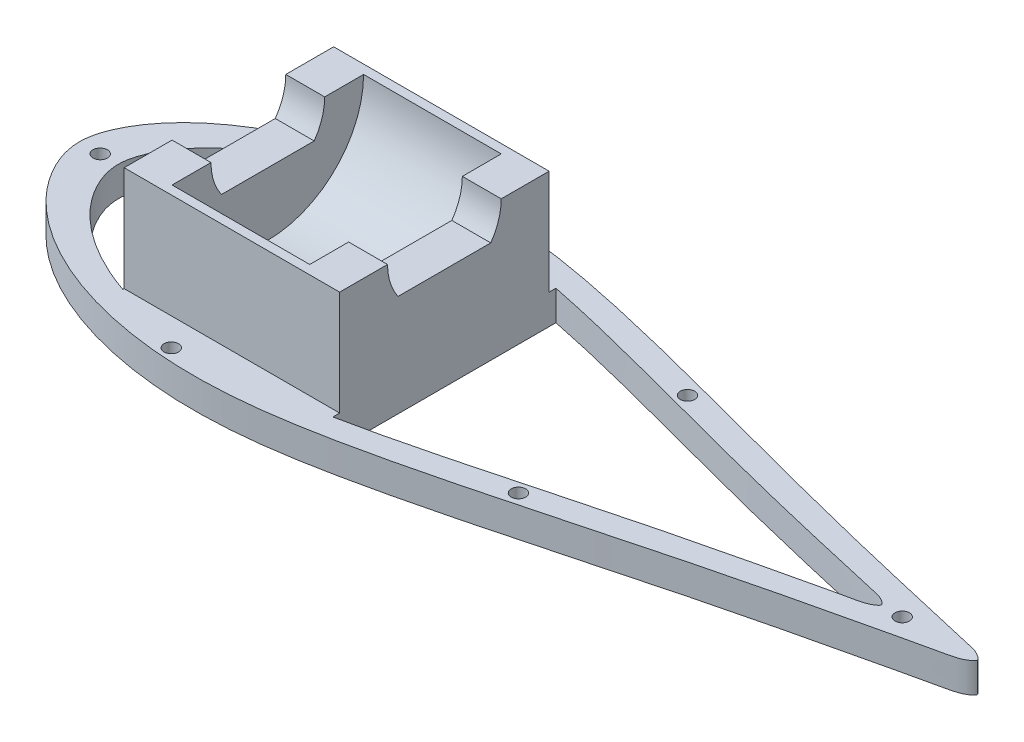
SolidWorks part; units mm, degrees
material "6061 Alloy"
ref_plane "Front Plane" through (0, 0, 0) normal (0, 0, 1) x (1, 0, 0)
ref_plane "Top Plane" through (0, 0, 0) normal (0, 1, 0) x (1, 0, 0)
ref_plane "Right Plane" through (0, 0, 0) normal (1, 0, 0) x (0, 0, -1)
curve "Curve2"
  spline degree 3 poles (0.6483, 0, -5.7987) (-0.3085, 0, 0) (0.6483, 0, 5.7987) (3.0311, 0, 11.5336) (6.6533, 0, 17.267) (11.4717, 0, 22.8371) (17.4302, 0, 28.1154) (24.4659, 0, 32.9986) (32.5279, 0, 37.3723) (41.5389, 0, 41.1607) (51.4314, 0, 44.2651) (62.1158, 0, 46.6282) (73.526, 0, 48.1549) (85.6114, 0, 48.7284) (98.3426, 0, 48.3105) (111.7257, 0, 46.8479) (125.7606, 0, 44.4122) (140.4343, 0, 41.2887) (155.6347, 0, 37.6615) (171.177, 0, 33.6995) (186.8539, 0, 29.5664) (202.4318, 0, 25.4194) (217.9957, 0, 21.2663) (233.2084, 0, 17.405) (247.6838, 0, 13.8748) (260.7251, 0, 10.7897) (272.1052, 0, 8.143) (281.7116, 0, 5.9794) (289.2075, 0, 4.169) (295.0367, 0, 3.0969) (298.1709, 0, 1.895) (300.5776, 0, 0) (298.1709, 0, -1.895) (295.0367, 0, -3.0969) (289.2075, 0, -4.169) (281.7116, 0, -5.9794) (272.1052, 0, -8.143) (260.7251, 0, -10.7897) (247.6838, 0, -13.8748) (233.2084, 0, -17.405) (217.9957, 0, -21.2663) (202.4318, 0, -25.4194) (186.8539, 0, -29.5664) (171.177, 0, -33.6995) (155.6347, 0, -37.6615) (140.4343, 0, -41.2887) (125.7606, 0, -44.4122) (111.7257, 0, -46.8479) (98.3426, 0, -48.3105) (85.6114, 0, -48.7284) (73.526, 0, -48.1549) (62.1158, 0, -46.6282) (51.4314, 0, -44.2651) (41.5389, 0, -41.1607) (32.5279, 0, -37.3723) (24.4659, 0, -32.9986) (17.4302, 0, -28.1154) (11.4717, 0, -22.8371) (6.6533, 0, -17.267) (3.0311, 0, -11.5336) (0.6483, 0, -5.7987) (-0.3085, 0, 0) (0.6483, 0, 5.7987) knots -0.028335 -0.018012 -0.008569 0 0.008569 0.018012 0.028335 0.039554 0.051691 0.064762 0.078763 0.093696 0.109541 0.126268 0.143841 0.162293 0.181715 0.202223 0.224008 0.247042 0.271046 0.295702 0.320629 0.34543 0.369662 0.394535 0.417436 0.438027 0.456004 0.47109 0.483065 0.49175 0.497395 0.5 0.502605 0.50825 0.516935 0.52891 0.543996 0.561973 0.582564 0.605465 0.630338 0.65457 0.679371 0.704298 0.728954 0.752958 0.775992 0.797777 0.818285 0.837707 0.856159 0.873732 0.890459 0.906304 0.921237 0.935238 0.948309 0.960446 0.971665 0.981988 0.991431 1 1.008569 1.018012 1.028335 periodic
sketch "Sketch3" plane through (0, 0, 0) normal (0, 1, 0) x (1, 0, 0)
  spline S0 degree 3 poles (0.6483, 5.7987) (-0.3085, 0) (0.6483, -5.7987) (3.0311, -11.5336) (6.6533, -17.267) (11.4717, -22.8371) (17.4302, -28.1154) (24.4659, -32.9986) (32.5279, -37.3723) (41.5389, -41.1607) (51.4314, -44.2651) (62.1158, -46.6282) (73.526, -48.1549) (85.6114, -48.7284) (98.3426, -48.3105) (111.7257, -46.8479) (125.7606, -44.4122) (140.4343, -41.2887) (155.6347, -37.6615) (171.177, -33.6995) (186.8539, -29.5664) (202.4318, -25.4194) (217.9957, -21.2663) (233.2084, -17.405) (247.6838, -13.8748) (260.7251, -10.7897) (272.1052, -8.143) (281.7116, -5.9794) (289.2075, -4.169) (295.0367, -3.0969) (298.1709, -1.895) (300.5776, 0) (298.1709, 1.895) (295.0367, 3.0969) (289.2075, 4.169) (281.7116, 5.9794) (272.1052, 8.143) (260.7251, 10.7897) (247.6838, 13.8748) (233.2084, 17.405) (217.9957, 21.2663) (202.4318, 25.4194) (186.8539, 29.5664) (171.177, 33.6995) (155.6347, 37.6615) (140.4343, 41.2887) (125.7606, 44.4122) (111.7257, 46.8479) (98.3426, 48.3105) (85.6114, 48.7284) (73.526, 48.1549) (62.1158, 46.6282) (51.4314, 44.2651) (41.5389, 41.1607) (32.5279, 37.3723) (24.4659, 32.9986) (17.4302, 28.1154) (11.4717, 22.8371) (6.6533, 17.267) (3.0311, 11.5336) (0.6483, 5.7987) (-0.3085, 0) (0.6483, -5.7987) knots -0.028335 -0.018012 -0.008569 0 0.008569 0.018012 0.028335 0.039554 0.051691 0.064762 0.078763 0.093696 0.109541 0.126268 0.143841 0.162293 0.181715 0.202223 0.224008 0.247042 0.271046 0.295702 0.320629 0.34543 0.369662 0.394535 0.417436 0.438027 0.456004 0.47109 0.483065 0.49175 0.497395 0.5 0.502605 0.50825 0.516935 0.52891 0.543996 0.561973 0.582564 0.605465 0.630338 0.65457 0.679371 0.704298 0.728954 0.752958 0.775992 0.797777 0.818285 0.837707 0.856159 0.873732 0.890459 0.906304 0.921237 0.935238 0.948309 0.960446 0.971665 0.981988 0.991431 1 1.008569 1.018012 1.028335 only from (0, 0) to (0, 0) construction
  spline S1 degree 3 poles (0.6483, 5.7987) (-0.3085, 0) (0.6483, -5.7987) (3.0311, -11.5336) (6.6533, -17.267) (11.4717, -22.8371) (17.4302, -28.1154) (24.4659, -32.9986) (32.5279, -37.3723) (41.5389, -41.1607) (51.4314, -44.2651) (62.1158, -46.6282) (73.526, -48.1549) (85.6114, -48.7284) (98.3426, -48.3105) (111.7257, -46.8479) (125.7606, -44.4122) (140.4343, -41.2887) (155.6347, -37.6615) (171.177, -33.6995) (186.8539, -29.5664) (202.4318, -25.4194) (217.9957, -21.2663) (233.2084, -17.405) (247.6838, -13.8748) (260.7251, -10.7897) (272.1052, -8.143) (281.7116, -5.9794) (289.2075, -4.169) (295.0367, -3.0969) (298.1709, -1.895) (300.5776, 0) (298.1709, 1.895) (295.0367, 3.0969) (289.2075, 4.169) (281.7116, 5.9794) (272.1052, 8.143) (260.7251, 10.7897) (247.6838, 13.8748) (233.2084, 17.405) (217.9957, 21.2663) (202.4318, 25.4194) (186.8539, 29.5664) (171.177, 33.6995) (155.6347, 37.6615) (140.4343, 41.2887) (125.7606, 44.4122) (111.7257, 46.8479) (98.3426, 48.3105) (85.6114, 48.7284) (73.526, 48.1549) (62.1158, 46.6282) (51.4314, 44.2651) (41.5389, 41.1607) (32.5279, 37.3723) (24.4659, 32.9986) (17.4302, 28.1154) (11.4717, 22.8371) (6.6533, 17.267) (3.0311, 11.5336) (0.6483, 5.7987) (-0.3085, 0) (0.6483, -5.7987) knots -0.028335 -0.018012 -0.008569 0 0.008569 0.018012 0.028335 0.039554 0.051691 0.064762 0.078763 0.093696 0.109541 0.126268 0.143841 0.162293 0.181715 0.202223 0.224008 0.247042 0.271046 0.295702 0.320629 0.34543 0.369662 0.394535 0.417436 0.438027 0.456004 0.47109 0.483065 0.49175 0.497395 0.5 0.502605 0.50825 0.516935 0.52891 0.543996 0.561973 0.582564 0.605465 0.630338 0.65457 0.679371 0.704298 0.728954 0.752958 0.775992 0.797777 0.818285 0.837707 0.856159 0.873732 0.890459 0.906304 0.921237 0.935238 0.948309 0.960446 0.971665 0.981988 0.991431 1 1.008569 1.018012 1.028335 only from (0, 0) to (0, 0)
extrude "Boss-Extrude1" add sketch "Sketch3" along normal blind 10
sketch "Sketch4" plane through (0, 0, 0) normal (0, -1, 0) x (1, 0, 0)
  spline S1 degree 3 poles (299.9957, 0.014) (299.9938, -0.0895) (299.9638, -0.2086) (299.9031, -0.3373) (299.8291, -0.4596) (299.7174, -0.5996) (299.5918, -0.7263) (299.4861, -0.8218) (299.4046, -0.8909) (299.3213, -0.9578) (299.2087, -1.0447) (299.0654, -1.1499) (298.8903, -1.2715) (298.7126, -1.3891) (298.3525, -1.6168) (297.92, -1.8622) (297.411, -2.1134) (297.0223, -2.287) (296.6272, -2.4451) (296.2267, -2.5893) (295.822, -2.722) (295.4141, -2.8452) (295.0041, -2.961) (294.5925, -3.0704) (294.0419, -3.2092) (293.4889, -3.3386) (292.9344, -3.4614) (292.5179, -3.5509) (292.101, -3.6386) (291.5448, -3.754) (290.9884, -3.8677) (290.4319, -3.9815) (289.8757, -4.0959) (289.1809, -4.2414) (288.3483, -4.4216) (286.6852, -4.7905) (284.1958, -5.3676) (281.4314, -6.0157) (279.2189, -6.5298) (277.0055, -7.0405) (274.7915, -7.5479) (272.5773, -8.0547) (270.9166, -8.4349) (269.2562, -8.816) (267.0427, -9.3258) (264.2767, -9.9669) (259.8527, -10.9999) (254.3255, -12.3029) (248.8019, -13.6215) (244.3858, -14.6874) (239.9714, -15.7609) (234.4573, -17.1179) (228.9488, -18.4974) (224.5457, -19.6156) (217.945, -21.3082) (208.0596, -23.9078) (194.8919, -27.424) (183.9159, -30.3428) (175.1284, -32.6526) (166.3345, -34.9377) (158.628, -36.8918) (152.0088, -38.511) (148.6961, -39.3081) (145.3801, -40.0913) (142.0605, -40.8591) (138.737, -41.6097) (135.4091, -42.3409) (132.0764, -43.0503) (127.626, -43.9641) (122.0492, -45.0405) (113.0926, -46.5738) (104.0773, -47.7374) (95.0123, -48.3913) (88.1991, -48.6052) (81.3834, -48.5233) (74.5794, -48.1282) (67.8019, -47.4032) (61.0693, -46.3378) (54.4011, -44.9234) (47.8168, -43.1503) (41.3469, -40.998) (35.028, -38.4414) (28.8957, -35.456) (23.013, -32.0075) (18.3744, -28.7213) (14.8691, -25.8285) (12.3582, -23.5227) (9.984, -21.0765) (8.1373, -18.9185) (6.7509, -17.1189) (5.7603, -15.7327) (4.8235, -14.3098) (3.9449, -12.8503) (3.2654, -11.6036) (2.7565, -10.5882) (2.0291, -9.0471) (1.0809, -6.6677) (0.2183, -3.3645) (-0.1054, 0.0396) (0.2336, 3.4379) (0.961, 6.1924) (1.7397, 8.3272) (2.4132, 9.8934) (3.1645, 11.4234) (3.9845, 12.9173) (4.8661, 14.375) (6.1184, 16.2702) (8.4977, 19.4595) (11.5773, 22.8096) (14.9283, 25.8792) (17.5601, 28.0457) (20.2943, 30.0805) (22.6482, 31.6695) (24.5714, 32.8789) (26.5195, 34.0477) (29.9892, 35.9887) (35.0983, 38.4733) (41.419, 41.0252) (46.8122, 42.8146) (51.1842, 44.0565) (55.5891, 45.1756) (63.3708, 46.8228) (74.6452, 48.3036) (88.2816, 48.7503) (101.9024, 48.0274) (113.1705, 46.5598) (122.1264, 45.0264) (128.8176, 43.735) (135.487, 42.3362) (142.1376, 40.8488) (148.7724, 39.2926) (157.6025, 37.1514) (173.0143, 33.2397) (190.5764, 28.5711) (208.1372, 23.899) (221.3117, 20.4089) (234.5313, 17.0929) (245.5623, 14.3906) (254.4011, 12.2854) (261.0337, 10.722) (266.5649, 9.436) (270.9921, 8.4173) (274.3131, 7.6559) (277.6343, 6.8948) (280.9537, 6.1266) (284.2713, 5.3501) (287.59, 4.5785) (290.368, 3.9915) (292.5952, 3.5417) (294.2576, 3.1677) (295.6314, 2.798) (296.7027, 2.4227) (297.4846, 2.0873) (298.1125, 1.7565) (298.5991, 1.4632) (298.8968, 1.2692) (299.1297, 1.1058) (299.3003, 0.9778) (299.438, 0.8649) (299.5442, 0.7698) (299.6215, 0.6957) (299.6958, 0.6184) (299.7894, 0.5104) (299.8729, 0.3935) (299.9377, 0.2672) (299.9677, 0.1847) (299.984, 0.117) (299.9921, 0.0657) (299.9957, 0.014) (299.9938, -0.0895) (299.9638, -0.2086) knots -0.000244 -0.000163 -0.000081 0 0.000326 0.000488 0.000651 0.000977 0.001302 0.001465 0.001628 0.00179 0.001953 0.002279 0.002604 0.00293 0.003255 0.004557 0.005208 0.005859 0.00651 0.007161 0.007812 0.008464 0.009115 0.009766 0.010417 0.011719 0.01237 0.013021 0.013672 0.014323 0.015625 0.016276 0.016927 0.018229 0.019531 0.020833 0.026042 0.03125 0.033854 0.036458 0.041667 0.044271 0.046875 0.049479 0.052083 0.057292 0.0625 0.072917 0.083333 0.088542 0.09375 0.104167 0.114583 0.119792 0.125 0.145833 0.166667 0.1875 0.197917 0.208333 0.229167 0.234375 0.239583 0.244792 0.25 0.255208 0.260417 0.265625 0.270833 0.28125 0.291667 0.3125 0.322917 0.333333 0.34375 0.354167 0.364583 0.375 0.385417 0.395833 0.40625 0.416667 0.427083 0.4375 0.447917 0.453125 0.458333 0.463542 0.46875 0.471354 0.473958 0.476562 0.479167 0.481771 0.483073 0.484375 0.489583 0.494792 0.5 0.505208 0.510417 0.513021 0.515625 0.518229 0.520833 0.523438 0.526042 0.53125 0.541667 0.546875 0.552083 0.557292 0.5625 0.565104 0.567708 0.572917 0.583333 0.59375 0.604167 0.609375 0.614583 0.625 0.645833 0.666667 0.6875 0.708333 0.71875 0.729167 0.739583 0.75 0.760417 0.770833 0.791667 0.833333 0.854167 0.875 0.895833 0.916667 0.927083 0.9375 0.947917 0.953125 0.958333 0.963542 0.96875 0.973958 0.979167 0.984375 0.986979 0.989583 0.992188 0.99349 0.994792 0.996094 0.996745 0.997396 0.997721 0.998047 0.998372 0.998535 0.998698 0.998861 0.999023 0.999349 0.999512 0.999674 0.999756 0.999837 0.999919 1 1.000326 1.000488 1.000651 only from (299.9939, -0.0377) to (299.9939, -0.0377)
  spline S3 degree 3 poles (299.9957, 0.014) (299.9938, -0.0895) (299.9638, -0.2086) (299.9031, -0.3373) (299.8291, -0.4596) (299.7174, -0.5996) (299.5918, -0.7263) (299.4861, -0.8218) (299.4046, -0.8909) (299.3213, -0.9578) (299.2087, -1.0447) (299.0654, -1.1499) (298.8903, -1.2715) (298.7126, -1.3891) (298.3525, -1.6168) (297.92, -1.8622) (297.411, -2.1134) (297.0223, -2.287) (296.6272, -2.4451) (296.2267, -2.5893) (295.822, -2.722) (295.4141, -2.8452) (295.0041, -2.961) (294.5925, -3.0704) (294.0419, -3.2092) (293.4889, -3.3386) (292.9344, -3.4614) (292.5179, -3.5509) (292.101, -3.6386) (291.5448, -3.754) (290.9884, -3.8677) (290.4319, -3.9815) (289.8757, -4.0959) (289.1809, -4.2414) (288.3483, -4.4216) (286.6852, -4.7905) (284.1958, -5.3676) (281.4314, -6.0157) (279.2189, -6.5298) (277.0055, -7.0405) (274.7915, -7.5479) (272.5773, -8.0547) (270.9166, -8.4349) (269.2562, -8.816) (267.0427, -9.3258) (264.2767, -9.9669) (259.8527, -10.9999) (254.3255, -12.3029) (248.8019, -13.6215) (244.3858, -14.6874) (239.9714, -15.7609) (234.4573, -17.1179) (228.9488, -18.4974) (224.5457, -19.6156) (217.945, -21.3082) (208.0596, -23.9078) (194.8919, -27.424) (183.9159, -30.3428) (175.1284, -32.6526) (166.3345, -34.9377) (158.628, -36.8918) (152.0088, -38.511) (148.6961, -39.3081) (145.3801, -40.0913) (142.0605, -40.8591) (138.737, -41.6097) (135.4091, -42.3409) (132.0764, -43.0503) (127.626, -43.9641) (122.0492, -45.0405) (113.0926, -46.5738) (104.0773, -47.7374) (95.0123, -48.3913) (88.1991, -48.6052) (81.3834, -48.5233) (74.5794, -48.1282) (67.8019, -47.4032) (61.0693, -46.3378) (54.4011, -44.9234) (47.8168, -43.1503) (41.3469, -40.998) (35.028, -38.4414) (28.8957, -35.456) (23.013, -32.0075) (18.3744, -28.7213) (14.8691, -25.8285) (12.3582, -23.5227) (9.984, -21.0765) (8.1373, -18.9185) (6.7509, -17.1189) (5.7603, -15.7327) (4.8235, -14.3098) (3.9449, -12.8503) (3.2654, -11.6036) (2.7565, -10.5882) (2.0291, -9.0471) (1.0809, -6.6677) (0.2183, -3.3645) (-0.1054, 0.0396) (0.2336, 3.4379) (0.961, 6.1924) (1.7397, 8.3272) (2.4132, 9.8934) (3.1645, 11.4234) (3.9845, 12.9173) (4.8661, 14.375) (6.1184, 16.2702) (8.4977, 19.4595) (11.5773, 22.8096) (14.9283, 25.8792) (17.5601, 28.0457) (20.2943, 30.0805) (22.6482, 31.6695) (24.5714, 32.8789) (26.5195, 34.0477) (29.9892, 35.9887) (35.0983, 38.4733) (41.419, 41.0252) (46.8122, 42.8146) (51.1842, 44.0565) (55.5891, 45.1756) (63.3708, 46.8228) (74.6452, 48.3036) (88.2816, 48.7503) (101.9024, 48.0274) (113.1705, 46.5598) (122.1264, 45.0264) (128.8176, 43.735) (135.487, 42.3362) (142.1376, 40.8488) (148.7724, 39.2926) (157.6025, 37.1514) (173.0143, 33.2397) (190.5764, 28.5711) (208.1372, 23.899) (221.3117, 20.4089) (234.5313, 17.0929) (245.5623, 14.3906) (254.4011, 12.2854) (261.0337, 10.722) (266.5649, 9.436) (270.9921, 8.4173) (274.3131, 7.6559) (277.6343, 6.8948) (280.9537, 6.1266) (284.2713, 5.3501) (287.59, 4.5785) (290.368, 3.9915) (292.5952, 3.5417) (294.2576, 3.1677) (295.6314, 2.798) (296.7027, 2.4227) (297.4846, 2.0873) (298.1125, 1.7565) (298.5991, 1.4632) (298.8968, 1.2692) (299.1297, 1.1058) (299.3003, 0.9778) (299.438, 0.8649) (299.5442, 0.7698) (299.6215, 0.6957) (299.6958, 0.6184) (299.7894, 0.5104) (299.8729, 0.3935) (299.9377, 0.2672) (299.9677, 0.1847) (299.984, 0.117) (299.9921, 0.0657) (299.9957, 0.014) (299.9938, -0.0895) (299.9638, -0.2086) knots -0.000244 -0.000163 -0.000081 0 0.000326 0.000488 0.000651 0.000977 0.001302 0.001465 0.001628 0.00179 0.001953 0.002279 0.002604 0.00293 0.003255 0.004557 0.005208 0.005859 0.00651 0.007161 0.007812 0.008464 0.009115 0.009766 0.010417 0.011719 0.01237 0.013021 0.013672 0.014323 0.015625 0.016276 0.016927 0.018229 0.019531 0.020833 0.026042 0.03125 0.033854 0.036458 0.041667 0.044271 0.046875 0.049479 0.052083 0.057292 0.0625 0.072917 0.083333 0.088542 0.09375 0.104167 0.114583 0.119792 0.125 0.145833 0.166667 0.1875 0.197917 0.208333 0.229167 0.234375 0.239583 0.244792 0.25 0.255208 0.260417 0.265625 0.270833 0.28125 0.291667 0.3125 0.322917 0.333333 0.34375 0.354167 0.364583 0.375 0.385417 0.395833 0.40625 0.416667 0.427083 0.4375 0.447917 0.453125 0.458333 0.463542 0.46875 0.471354 0.473958 0.476562 0.479167 0.481771 0.483073 0.484375 0.489583 0.494792 0.5 0.505208 0.510417 0.513021 0.515625 0.518229 0.520833 0.523438 0.526042 0.53125 0.541667 0.546875 0.552083 0.557292 0.5625 0.565104 0.567708 0.572917 0.583333 0.59375 0.604167 0.609375 0.614583 0.625 0.645833 0.666667 0.6875 0.708333 0.71875 0.729167 0.739583 0.75 0.760417 0.770833 0.791667 0.833333 0.854167 0.875 0.895833 0.916667 0.927083 0.9375 0.947917 0.953125 0.958333 0.963542 0.96875 0.973958 0.979167 0.984375 0.986979 0.989583 0.992188 0.99349 0.994792 0.996094 0.996745 0.997396 0.997721 0.998047 0.998372 0.998535 0.998698 0.998861 0.999023 0.999349 0.999512 0.999674 0.999756 0.999837 0.999919 1 1.000326 1.000488 1.000651 only from (299.9939, -0.0377) to (299.9939, -0.0377)
  point P0 (0, 0)
sketch "Sketch5" plane through (0, 10, 0) normal (0, 1, 0) x (1, 0, 0)
  line L0 (0, 0) -> (300, 0) construction
  line L1 (50, 35) -> (122, 35)
  line L2 (50, 35) -> (50, -35)
  line L3 (50, -35) -> (122, -35)
  line L4 (122, 35) -> (122, -35)
  spline S0 degree 3 poles (0.6483, 5.7987) (-0.3085, 0) (0.6483, -5.7987) (3.0311, -11.5336) (6.6533, -17.267) (11.4717, -22.8371) (17.4302, -28.1154) (24.4659, -32.9986) (32.5279, -37.3723) (41.5389, -41.1607) (51.4314, -44.2651) (62.1158, -46.6282) (73.526, -48.1549) (85.6114, -48.7284) (98.3426, -48.3105) (111.7257, -46.8479) (125.7606, -44.4122) (140.4343, -41.2887) (155.6347, -37.6615) (171.177, -33.6995) (186.8539, -29.5664) (202.4318, -25.4194) (217.9957, -21.2663) (233.2084, -17.405) (247.6838, -13.8748) (260.7251, -10.7897) (272.1052, -8.143) (281.7116, -5.9794) (289.2075, -4.169) (295.0367, -3.0969) (298.1709, -1.895) (300.5776, 0) (298.1709, 1.895) (295.0367, 3.0969) (289.2075, 4.169) (281.7116, 5.9794) (272.1052, 8.143) (260.7251, 10.7897) (247.6838, 13.8748) (233.2084, 17.405) (217.9957, 21.2663) (202.4318, 25.4194) (186.8539, 29.5664) (171.177, 33.6995) (155.6347, 37.6615) (140.4343, 41.2887) (125.7606, 44.4122) (111.7257, 46.8479) (98.3426, 48.3105) (85.6114, 48.7284) (73.526, 48.1549) (62.1158, 46.6282) (51.4314, 44.2651) (41.5389, 41.1607) (32.5279, 37.3723) (24.4659, 32.9986) (17.4302, 28.1154) (11.4717, 22.8371) (6.6533, 17.267) (3.0311, 11.5336) (0.6483, 5.7987) (-0.3085, 0) (0.6483, -5.7987) knots -0.028335 -0.018012 -0.008569 0 0.008569 0.018012 0.028335 0.039554 0.051691 0.064762 0.078763 0.093696 0.109541 0.126268 0.143841 0.162293 0.181715 0.202223 0.224008 0.247042 0.271046 0.295702 0.320629 0.34543 0.369662 0.394535 0.417436 0.438027 0.456004 0.47109 0.483065 0.49175 0.497395 0.5 0.502605 0.50825 0.516935 0.52891 0.543996 0.561973 0.582564 0.605465 0.630338 0.65457 0.679371 0.704298 0.728954 0.752958 0.775992 0.797777 0.818285 0.837707 0.856159 0.873732 0.890459 0.906304 0.921237 0.935238 0.948309 0.960446 0.971665 0.981988 0.991431 1 1.008569 1.018012 1.028335 only from (0, 0) to (0, 0) construction
  dimension "D1" = 70
  dimension "D2" = 72
  dimension "D3" = 35
  dimension "D4" = 50
extrude "Boss-Extrude2" add sketch "Sketch5" along normal blind 70
sketch "Sketch6" plane through (50, 0, 0) normal (-1, 0, 0) x (0, 0, 1)
  line L0 (-15.4919, 56) -> (15.4919, 56)
  line L1 (15.4919, 34) -> (-15.4919, 34)
  line L2 (0, 80) -> (0, 10) construction
  line L3 (-35, 80) -> (35, 80) construction
  line L4 (48.5664, 10) -> (-48.5664, 10) construction
  line L5 (-35, 45) -> (35, 45)
  line L6 (-35, 80) -> (-35, 10) construction
  line L7 (35, 80) -> (35, 10) construction
  line L8 (-35, 45) -> (-35, 80)
  line L9 (-35, 80) -> (35, 80)
  line L10 (35, 80) -> (35, 45)
  line L11 (-19, 45) -> (19, 45)
  circle A0 centre (0, 45) radius 32
  circle A1 centre (0, 45) radius 19
  arc A2 (-15.4919, 56) -> (-15.4919, 34) centre (0, 45) ccw
  arc A3 (15.4919, 56) -> (15.4919, 34) centre (0, 45) cw
  line M2 (35, 10) -> (35, 80)
  line M3 (35, 80) -> (-35, 80)
  line M4 (-35, 80) -> (-35, 10)
extrude "Cut-Extrude3" cut sketch "Sketch6" against normal up to surface (72 mm away) contours L2 L9 L5 A0 M4 | L2 A0 L5 M3 M2 | A0 L2 A1 L5 | L2 A0 L5 A1 | L2 A1 L0 | A1 L2 L0 | L0 L2 L5 A1 | L2 L0 A1 L5
sketch "Sketch7" plane through (50, 0, 0) normal (-1, 0, 0) x (0, 0, 1)
  line L0 (-15.4919, 56) -> (15.4919, 56)
  line L1 (15.4919, 34) -> (-15.4919, 34)
  line L2 (-19, 45) -> (19, 45)
  circle A0 centre (0, 45) radius 32
  circle A1 centre (0, 45) radius 19
  arc A2 (-15.4919, 56) -> (-15.4919, 34) centre (0, 45) ccw
  arc A3 (15.4919, 56) -> (15.4919, 34) centre (0, 45) cw
  line M2 (35, 45) -> (-35, 45)
extrude "Cut-Extrude4" cut sketch "Sketch7" against normal blind 13 contours A1 L1 M2
sketch "Sketch8" plane through (63, 0, 0) normal (-1, 0, 0) x (0, 0, 1)
  line L0 (-15.4919, 56) -> (15.4919, 56)
  line L1 (15.4919, 34) -> (-15.4919, 34)
  line L2 (-19, 45) -> (19, 45)
  line L3 (-19, 45) -> (19, 45)
  circle A0 centre (0, 45) radius 32
  circle A1 centre (0, 45) radius 19
  arc A2 (-15.4919, 56) -> (-15.4919, 34) centre (0, 45) ccw
  arc A3 (15.4919, 56) -> (15.4919, 34) centre (0, 45) cw
  line M1 (19, 45) -> (-19, 45)
  arc M2 (-19, 45) -> (-15.4919, 34) centre (0, 45) ccw
  line M3 (-15.4919, 34) -> (15.4919, 34)
  arc M4 (15.4919, 34) -> (19, 45) centre (0, 45) ccw
extrude "Cut-Extrude5" cut sketch "Sketch8" against normal blind 46 contours M4 M1 M2 M3 | A1 M3 | A0 A1 M4 M2
sketch "Sketch9" plane through (122, 0, 0) normal (1, 0, 0) x (0, 0, -1)
  line L0 (-15.4919, 56) -> (15.4919, 56)
  line L1 (15.4919, 34) -> (-15.4919, 34)
  line L2 (-19, 45) -> (19, 45)
  line L3 (35, 45) -> (-35, 45)
  circle A0 centre (0, 45) radius 32
  circle A1 centre (0, 45) radius 19
  arc A2 (-15.4919, 56) -> (-15.4919, 34) centre (0, 45) ccw
  arc A3 (15.4919, 56) -> (15.4919, 34) centre (0, 45) cw
  line M2 (35, 45) -> (-35, 45)
extrude "Cut-Extrude6" cut sketch "Sketch9" against normal blind 13 contours A1 L1 M2
sketch "Sketch10" plane through (0, 10, 0) normal (0, 1, 0) x (1, 0, 0)
  line L0 (299.9938, 0.0376) -> (0, 0) construction
  line L1 (50, -35) -> (50, -35.4385)
  line L2 (50, -35) -> (122, -35)
  line L3 (122, -35) -> (122, -37.252)
  line L4 (122, 35) -> (122, 37.263)
  line L5 (122, 35) -> (50, 35)
  line L6 (50, 35) -> (50, 35.4503)
  spline S0 degree 3 poles (299.989, 0.0891) (299.9965, 0.0205) (299.9943, -0.0659) (299.9772, -0.151) (299.9506, -0.2343) (299.9223, -0.299) (299.88, -0.3772) (299.8316, -0.4524) (299.7445, -0.5663) (299.6471, -0.6713) (299.5439, -0.7698) (299.4641, -0.8409) (299.3823, -0.9095) (299.2153, -1.0425) (298.9554, -1.2294) (298.6587, -1.4246) (298.4169, -1.5735) (298.1723, -1.7175) (297.8614, -1.8884) (297.4808, -2.079) (297.0933, -2.2548) (296.6995, -2.4161) (296.3003, -2.5636) (295.7621, -2.7443) (295.0807, -2.945) (294.2561, -3.1597) (293.427, -3.3556) (292.3173, -3.5986) (290.368, -3.9912) (287.5897, -4.5777) (284.2714, -5.3508) (280.9537, -6.1266) (277.6343, -6.895) (274.3132, -7.656) (270.9921, -8.4174) (268.2251, -9.0539) (266.012, -9.5656) (262.6929, -10.3357) (258.8223, -11.2413) (253.2958, -12.5472) (247.7722, -13.8653) (241.1492, -15.4692) (232.3266, -17.6406) (221.3152, -20.4224) (208.1347, -23.889) (197.1618, -26.8196) (188.3815, -29.1564) (181.7943, -30.9017) (175.2037, -32.6341) (168.6082, -34.3478) (162.006, -36.0355) (153.1913, -38.2386) (144.355, -40.3552) (135.4872, -42.3361) (128.8175, -43.7343) (122.1252, -45.0268) (113.1689, -46.5624) (101.901, -48.0213) (88.2784, -48.753) (74.6442, -48.3004) (63.3688, -46.8222) (54.4769, -44.9415) (47.8924, -43.1718) (41.4199, -41.0246) (32.9936, -37.6224) (24.9364, -33.3619) (17.5084, -28.1114) (13.2067, -24.3908) (10.0355, -21.1344) (7.8152, -18.5481) (5.7776, -15.8148) (3.9548, -12.9354) (2.3746, -9.9105) (1.1062, -6.7423) (0.2343, -3.4411) (-0.0494, -0.6057) (0.0563, 1.6619) (0.3647, 3.9118) (1.0814, 6.6676) (2.3448, 9.8395) (3.9144, 12.8679) (5.7335, 15.751) (7.4296, 18.0316) (8.8768, 19.7825) (10.0048, 21.0592) (11.1722, 22.2998) (13.5803, 24.71) (16.5896, 27.3176) (19.7756, 29.6953) (21.6416, 30.9901) (23.1809, 32.008) (24.865, 33.0636) (26.576, 34.075) (29.9193, 35.9501) (33.745, 37.8328) (38.1886, 39.7198) (42.4265, 41.3571) (47.8177, 43.1508) (54.4014, 44.9238) (63.2935, 46.8087) (72.3129, 47.9989) (81.3847, 48.5247) (87.0641, 48.5919) (91.0386, 48.51) (93.8761, 48.4068) (96.4283, 48.2744) (99.8276, 48.0388) (102.6562, 47.7878) (105.7626, 47.4625) (108.5825, 47.1294) (111.959, 46.6734) (116.4513, 45.9976) (120.9299, 45.2307) (125.3956, 44.394) (128.7389, 43.7362) (132.0766, 43.0512) (135.4092, 42.3417) (138.737, 41.6103) (143.1683, 40.609) (148.6976, 39.3141) (155.3195, 37.7061) (161.9305, 36.0533) (168.5328, 34.3656) (177.3269, 32.0812) (186.1113, 29.7598) (194.8915, 27.4224) (201.4759, 25.6665) (208.0611, 23.9139) (214.6498, 22.1745) (223.4425, 19.8857) (234.4538, 17.1036) (245.4879, 14.4125) (254.3255, 12.3028) (260.9581, 10.7388) (266.4889, 9.4516) (270.3631, 8.5616) (272.5773, 8.0549) (274.238, 7.675) (275.6218, 7.3581) (277.0056, 7.0406) (278.1123, 6.7858) (279.4955, 6.4659) (280.8783, 6.1442) (282.5369, 5.7553) (284.7486, 5.2377) (286.9617, 4.7256) (289.1803, 4.2391) (290.849, 3.8961) (292.5185, 3.555) (293.9057, 3.2484) (295.007, 2.9667) (295.825, 2.7277) (296.6302, 2.4505) (297.2835, 2.1747) (297.7925, 1.9239) (298.1667, 1.7212) (298.5331, 1.5039) (298.8312, 1.311) (299.0653, 1.1497) (299.2377, 1.0242) (299.4054, 0.8921) (299.5665, 0.7512) (299.693, 0.6242) (299.7857, 0.5148) (299.8491, 0.4283) (299.9045, 0.3369) (299.9494, 0.2407) (299.9758, 0.1572) (299.989, 0.0891) (299.9965, 0.0205) (299.9943, -0.0659) knots -0.000326 -0.000163 -0.000081 0 0.000163 0.000326 0.000407 0.00057 0.000651 0.000814 0.000977 0.001302 0.001465 0.001628 0.00179 0.001953 0.002604 0.003255 0.003581 0.003906 0.004557 0.005208 0.005859 0.00651 0.007161 0.007812 0.009115 0.010417 0.011719 0.013021 0.015625 0.020833 0.026042 0.03125 0.036458 0.041667 0.046875 0.052083 0.054688 0.057292 0.067708 0.072917 0.083333 0.09375 0.104167 0.125 0.145833 0.166667 0.177083 0.1875 0.197917 0.208333 0.21875 0.229167 0.25 0.260417 0.270833 0.28125 0.291667 0.3125 0.333333 0.354167 0.375 0.385417 0.395833 0.40625 0.416667 0.4375 0.447917 0.458333 0.463542 0.46875 0.473958 0.479167 0.484375 0.489583 0.494792 0.5 0.502604 0.505208 0.510417 0.515625 0.520833 0.526042 0.53125 0.533854 0.536458 0.539062 0.541667 0.552083 0.557292 0.559896 0.5625 0.565755 0.56901 0.571615 0.583333 0.588542 0.59375 0.604167 0.614583 0.625 0.645833 0.65625 0.666667 0.671875 0.674479 0.679688 0.683594 0.690104 0.692708 0.697917 0.703125 0.708333 0.71875 0.723958 0.729167 0.734375 0.739583 0.744792 0.75 0.760417 0.770833 0.78125 0.791667 0.802083 0.822917 0.833333 0.84375 0.854167 0.864583 0.875 0.895833 0.916667 0.927083 0.9375 0.947917 0.953125 0.955729 0.958333 0.960938 0.96224 0.964844 0.966146 0.96875 0.971354 0.973958 0.979167 0.981771 0.984375 0.986979 0.989583 0.990885 0.992188 0.99349 0.994792 0.995443 0.996094 0.996745 0.997396 0.997721 0.998047 0.998372 0.998698 0.999023 0.999186 0.999349 0.999512 0.999674 0.999837 0.999919 1 1.000163 1.000326 1.000407 only from (299.9938, 0.0376) to (299.9938, 0.0376)
  spline S1 degree 3 poles (299.989, 0.0891) (299.9965, 0.0205) (299.9943, -0.0659) (299.9772, -0.151) (299.9506, -0.2343) (299.9223, -0.299) (299.88, -0.3772) (299.8316, -0.4524) (299.7445, -0.5663) (299.6471, -0.6713) (299.5439, -0.7698) (299.4641, -0.8409) (299.3823, -0.9095) (299.2153, -1.0425) (298.9554, -1.2294) (298.6587, -1.4246) (298.4169, -1.5735) (298.1723, -1.7175) (297.8614, -1.8884) (297.4808, -2.079) (297.0933, -2.2548) (296.6995, -2.4161) (296.3003, -2.5636) (295.7621, -2.7443) (295.0807, -2.945) (294.2561, -3.1597) (293.427, -3.3556) (292.3173, -3.5986) (290.368, -3.9912) (287.5897, -4.5777) (284.2714, -5.3508) (280.9537, -6.1266) (277.6343, -6.895) (274.3132, -7.656) (270.9921, -8.4174) (268.2251, -9.0539) (266.012, -9.5656) (262.6929, -10.3357) (258.8223, -11.2413) (253.2958, -12.5472) (247.7722, -13.8653) (241.1492, -15.4692) (232.3266, -17.6406) (221.3152, -20.4224) (208.1347, -23.889) (197.1618, -26.8196) (188.3815, -29.1564) (181.7943, -30.9017) (175.2037, -32.6341) (168.6082, -34.3478) (162.006, -36.0355) (153.1913, -38.2386) (144.355, -40.3552) (135.4872, -42.3361) (128.8175, -43.7343) (122.1252, -45.0268) (113.1689, -46.5624) (101.901, -48.0213) (88.2784, -48.753) (74.6442, -48.3004) (63.3688, -46.8222) (54.4769, -44.9415) (47.8924, -43.1718) (41.4199, -41.0246) (32.9936, -37.6224) (24.9364, -33.3619) (17.5084, -28.1114) (13.2067, -24.3908) (10.0355, -21.1344) (7.8152, -18.5481) (5.7776, -15.8148) (3.9548, -12.9354) (2.3746, -9.9105) (1.1062, -6.7423) (0.2343, -3.4411) (-0.0494, -0.6057) (0.0563, 1.6619) (0.3647, 3.9118) (1.0814, 6.6676) (2.3448, 9.8395) (3.9144, 12.8679) (5.7335, 15.751) (7.4296, 18.0316) (8.8768, 19.7825) (10.0048, 21.0592) (11.1722, 22.2998) (13.5803, 24.71) (16.5896, 27.3176) (19.7756, 29.6953) (21.6416, 30.9901) (23.1809, 32.008) (24.865, 33.0636) (26.576, 34.075) (29.9193, 35.9501) (33.745, 37.8328) (38.1886, 39.7198) (42.4265, 41.3571) (47.8177, 43.1508) (54.4014, 44.9238) (63.2935, 46.8087) (72.3129, 47.9989) (81.3847, 48.5247) (87.0641, 48.5919) (91.0386, 48.51) (93.8761, 48.4068) (96.4283, 48.2744) (99.8276, 48.0388) (102.6562, 47.7878) (105.7626, 47.4625) (108.5825, 47.1294) (111.959, 46.6734) (116.4513, 45.9976) (120.9299, 45.2307) (125.3956, 44.394) (128.7389, 43.7362) (132.0766, 43.0512) (135.4092, 42.3417) (138.737, 41.6103) (143.1683, 40.609) (148.6976, 39.3141) (155.3195, 37.7061) (161.9305, 36.0533) (168.5328, 34.3656) (177.3269, 32.0812) (186.1113, 29.7598) (194.8915, 27.4224) (201.4759, 25.6665) (208.0611, 23.9139) (214.6498, 22.1745) (223.4425, 19.8857) (234.4538, 17.1036) (245.4879, 14.4125) (254.3255, 12.3028) (260.9581, 10.7388) (266.4889, 9.4516) (270.3631, 8.5616) (272.5773, 8.0549) (274.238, 7.675) (275.6218, 7.3581) (277.0056, 7.0406) (278.1123, 6.7858) (279.4955, 6.4659) (280.8783, 6.1442) (282.5369, 5.7553) (284.7486, 5.2377) (286.9617, 4.7256) (289.1803, 4.2391) (290.849, 3.8961) (292.5185, 3.555) (293.9057, 3.2484) (295.007, 2.9667) (295.825, 2.7277) (296.6302, 2.4505) (297.2835, 2.1747) (297.7925, 1.9239) (298.1667, 1.7212) (298.5331, 1.5039) (298.8312, 1.311) (299.0653, 1.1497) (299.2377, 1.0242) (299.4054, 0.8921) (299.5665, 0.7512) (299.693, 0.6242) (299.7857, 0.5148) (299.8491, 0.4283) (299.9045, 0.3369) (299.9494, 0.2407) (299.9758, 0.1572) (299.989, 0.0891) (299.9965, 0.0205) (299.9943, -0.0659) knots -0.000326 -0.000163 -0.000081 0 0.000163 0.000326 0.000407 0.00057 0.000651 0.000814 0.000977 0.001302 0.001465 0.001628 0.00179 0.001953 0.002604 0.003255 0.003581 0.003906 0.004557 0.005208 0.005859 0.00651 0.007161 0.007812 0.009115 0.010417 0.011719 0.013021 0.015625 0.020833 0.026042 0.03125 0.036458 0.041667 0.046875 0.052083 0.054688 0.057292 0.067708 0.072917 0.083333 0.09375 0.104167 0.125 0.145833 0.166667 0.177083 0.1875 0.197917 0.208333 0.21875 0.229167 0.25 0.260417 0.270833 0.28125 0.291667 0.3125 0.333333 0.354167 0.375 0.385417 0.395833 0.40625 0.416667 0.4375 0.447917 0.458333 0.463542 0.46875 0.473958 0.479167 0.484375 0.489583 0.494792 0.5 0.502604 0.505208 0.510417 0.515625 0.520833 0.526042 0.53125 0.533854 0.536458 0.539062 0.541667 0.552083 0.557292 0.559896 0.5625 0.565755 0.56901 0.571615 0.583333 0.588542 0.59375 0.604167 0.614583 0.625 0.645833 0.65625 0.666667 0.671875 0.674479 0.679688 0.683594 0.690104 0.692708 0.697917 0.703125 0.708333 0.71875 0.723958 0.729167 0.734375 0.739583 0.744792 0.75 0.760417 0.770833 0.78125 0.791667 0.802083 0.822917 0.833333 0.84375 0.854167 0.864583 0.875 0.895833 0.916667 0.927083 0.9375 0.947917 0.953125 0.955729 0.958333 0.960938 0.96224 0.964844 0.966146 0.96875 0.971354 0.973958 0.979167 0.981771 0.984375 0.986979 0.989583 0.990885 0.992188 0.99349 0.994792 0.995443 0.996094 0.996745 0.997396 0.997721 0.998047 0.998372 0.998698 0.999023 0.999186 0.999349 0.999512 0.999674 0.999837 0.999919 1 1.000163 1.000326 1.000407 only from (299.9938, 0.0376) to (299.9938, 0.0376)
  spline S2 degree 3 poles (267.9897, 0.0814) (267.9961, 0.0231) (267.9942, -0.0504) (267.9797, -0.1227) (267.9571, -0.1935) (267.933, -0.2485) (267.8971, -0.315) (267.8559, -0.3789) (267.7819, -0.4757) (267.6992, -0.5649) (267.6114, -0.6487) (267.5435, -0.7091) (267.474, -0.7674) (267.3321, -0.8805) (267.1111, -1.0393) (266.859, -1.2053) (266.6535, -1.3318) (266.4455, -1.4543) (266.1813, -1.5995) (265.8578, -1.7615) (265.5284, -1.911) (265.1936, -2.0481) (264.8543, -2.1734) (264.3968, -2.327) (263.8176, -2.4976) (263.1167, -2.6801) (262.4121, -2.8467) (261.4688, -3.0532) (259.8119, -3.3869) (257.4503, -3.8854) (254.6298, -4.5425) (251.8097, -5.2019) (248.9882, -5.8551) (246.1653, -6.502) (243.3424, -7.1492) (240.9904, -7.6902) (239.1092, -8.1252) (236.288, -8.7797) (232.9981, -9.5495) (228.3005, -10.6594) (223.6054, -11.7799) (217.9759, -13.1432) (210.4767, -14.9888) (201.117, -17.3534) (189.9136, -20.3) (180.5866, -22.791) (173.1233, -24.7773) (167.5242, -26.2608) (161.9222, -27.7334) (156.3161, -29.19) (150.7042, -30.6245) (143.2116, -32.4971) (135.7008, -34.2963) (128.1632, -35.98) (122.4939, -37.1685) (116.8055, -38.2672) (109.1926, -39.5724) (99.615, -40.8124) (88.0357, -41.4344) (76.4466, -41.0497) (66.8625, -39.7932) (59.3045, -38.1947) (53.7076, -36.6904) (48.206, -34.8652) (41.0436, -31.9734) (34.195, -28.352) (27.8812, -23.8891) (24.2248, -20.7265) (21.5293, -17.9586) (19.642, -15.7602) (17.91, -13.4369) (16.3606, -10.9894) (15.0175, -8.4183) (13.9394, -5.7253) (13.1982, -2.9193) (12.9571, -0.5092) (13.0469, 1.4183) (13.3091, 3.3307) (13.9182, 5.6731) (14.9922, 8.3693) (16.3263, 10.9434) (17.8726, 13.394) (19.3142, 15.3325) (20.5443, 16.8208) (21.5031, 17.906) (22.4955, 18.9605) (24.5424, 21.0092) (27.1002, 23.2256) (29.8083, 25.2466) (31.3945, 26.3472) (32.7029, 27.2125) (34.1343, 28.1097) (35.5887, 28.9694) (38.4305, 30.5632) (41.6824, 32.1635) (45.4594, 33.7675) (49.0616, 35.1592) (53.6441, 36.6838) (59.2402, 38.1909) (66.7985, 39.7931) (74.465, 40.8047) (82.1761, 41.2516) (87.0036, 41.3087) (90.3818, 41.2391) (92.7938, 41.1514) (94.9631, 41.0389) (97.8525, 40.8386) (100.2568, 40.6253) (102.8973, 40.3488) (105.2942, 40.0656) (108.1642, 39.678) (111.9827, 39.1036) (115.7895, 38.4517) (119.5853, 37.7406) (122.4271, 37.1814) (125.2642, 36.5991) (128.0969, 35.9961) (130.9255, 35.3744) (134.6921, 34.5233) (139.392, 33.4226) (145.0207, 32.0558) (150.64, 30.651) (156.2519, 29.2164) (163.727, 27.2747) (171.1937, 25.3015) (178.6569, 23.3147) (184.2536, 21.8222) (189.851, 20.3325) (195.4514, 18.854) (202.9252, 16.9085) (212.2848, 14.5437) (221.6638, 12.2562) (229.1758, 10.463) (234.8134, 9.1336) (239.5146, 8.0395) (242.8077, 7.283) (244.6898, 6.8523) (246.1014, 6.5294) (247.2776, 6.26) (248.4538, 5.9901) (249.3946, 5.7736) (250.5703, 5.5017) (251.7456, 5.2282) (253.1554, 4.8976) (255.0354, 4.4577) (256.9165, 4.0224) (258.8024, 3.6089) (260.2207, 3.3173) (261.6398, 3.0274) (262.8189, 2.7668) (263.755, 2.5273) (264.4503, 2.3242) (265.1347, 2.0885) (265.6901, 1.8542) (266.1227, 1.641) (266.4408, 1.4686) (266.7522, 1.284) (267.0056, 1.12) (267.2045, 0.9829) (267.3511, 0.8762) (267.4936, 0.7639) (267.6306, 0.6442) (267.7381, 0.5362) (267.8169, 0.4432) (267.8708, 0.3697) (267.9179, 0.292) (267.9561, 0.2102) (267.9785, 0.1393) (267.9897, 0.0814) (267.9961, 0.0231) (267.9942, -0.0504) knots -0.000326 -0.000163 -0.000081 0 0.000163 0.000326 0.000407 0.00057 0.000651 0.000814 0.000977 0.001302 0.001465 0.001628 0.00179 0.001953 0.002604 0.003255 0.003581 0.003906 0.004557 0.005208 0.005859 0.00651 0.007161 0.007812 0.009115 0.010417 0.011719 0.013021 0.015625 0.020833 0.026042 0.03125 0.036458 0.041667 0.046875 0.052083 0.054688 0.057292 0.067708 0.072917 0.083333 0.09375 0.104167 0.125 0.145833 0.166667 0.177083 0.1875 0.197917 0.208333 0.21875 0.229167 0.25 0.260417 0.270833 0.28125 0.291667 0.3125 0.333333 0.354167 0.375 0.385417 0.395833 0.40625 0.416667 0.4375 0.447917 0.458333 0.463542 0.46875 0.473958 0.479167 0.484375 0.489583 0.494792 0.5 0.502604 0.505208 0.510417 0.515625 0.520833 0.526042 0.53125 0.533854 0.536458 0.539062 0.541667 0.552083 0.557292 0.559896 0.5625 0.565755 0.56901 0.571615 0.583333 0.588542 0.59375 0.604167 0.614583 0.625 0.645833 0.65625 0.666667 0.671875 0.674479 0.679688 0.683594 0.690104 0.692708 0.697917 0.703125 0.708333 0.71875 0.723958 0.729167 0.734375 0.739583 0.744792 0.75 0.760417 0.770833 0.78125 0.791667 0.802083 0.822917 0.833333 0.84375 0.854167 0.864583 0.875 0.895833 0.916667 0.927083 0.9375 0.947917 0.953125 0.955729 0.958333 0.960938 0.96224 0.964844 0.966146 0.96875 0.971354 0.973958 0.979167 0.981771 0.984375 0.986979 0.989583 0.990885 0.992188 0.99349 0.994792 0.995443 0.996094 0.996745 0.997396 0.997721 0.998047 0.998372 0.998698 0.999023 0.999186 0.999349 0.999512 0.999674 0.999837 0.999919 1 1.000163 1.000326 1.000407 only from (267.9938, 0.0376) to (267.9938, 0.0376)
  line M2 (50, -35) -> (50, 35)
  line M4 (122, 35) -> (122, -35)
  dimension "D1" = 32
extrude "Cut-Extrude7" cut sketch "Sketch10" against normal blind 10 contours L0 L6 S2 M2 | L0 S2 L1 M2 | L0 S2 L4 M4 | S2 L0 L3 M4
sketch "Sketch12" plane through (0, 10, 0) normal (0, 1, 0) x (1, 0, 0)
  line L0 (0, 0) -> (300, 0)
  circle A0 centre (7, 0) radius 2.415
  circle A1 centre (275, 0) radius 2.415
  circle A2 centre (175, 28.25) radius 2.415
  circle A3 centre (75, 44.25) radius 2.415
  circle A4 centre (75, -44.25) radius 2.415
  circle A5 centre (175, -28.25) radius 2.415
  spline S0 degree 3 poles (0, 0) (0.0127, 0.8519) (0.0873, 2.1289) (0.3851, 3.8086) (0.6701, 5.0543) (1.0208, 6.2831) (1.4295, 7.4936) (1.8916, 8.6847) (2.5723, 10.2466) (3.3403, 11.7685) (4.1821, 13.2499) (4.8481, 14.3404) (5.5463, 15.4104) (6.5173, 16.8095) (8.3173, 19.1857) (11.1491, 22.3759) (14.254, 25.2986) (16.8696, 27.4832) (18.8904, 29.0471) (20.9656, 30.5381) (23.0907, 31.9578) (25.2609, 33.3081) (28.2091, 35.0179) (31.9867, 36.9901) (35.864, 38.7536) (40.2978, 40.5697) (43.6075, 41.7562) (47.2597, 42.9228) (49.1997, 43.4984) (51.5612, 44.1482) (53.6234, 44.6807) (56.9396, 45.4648) (61.1126, 46.32) (66.1561, 47.1501) (72.9181, 48.0008) (81.4191, 48.5904) (91.6468, 48.593) (101.8545, 47.9504) (112.0056, 46.7354) (122.0921, 45.0639) (132.1215, 43.0754) (142.1039, 40.8759) (150.3928, 38.912) (157.0105, 37.2863) (161.968, 36.0435) (166.9206, 34.7813) (171.869, 33.5031) (176.8142, 32.2122) (181.7567, 30.9112) (186.6972, 29.6027) (193.2828, 27.8512) (204.8052, 24.777) (217.9781, 21.2804) (231.1875, 17.9255) (241.1104, 15.4724) (251.047, 13.0749) (259.3371, 11.1171) (265.9742, 9.5723) (270.9544, 8.4242) (275.1062, 7.4744) (278.4271, 6.7123) (280.9168, 6.1366) (283.4056, 5.5565) (285.4789, 5.0702) (287.1394, 4.6894) (288.1786, 4.4576) (289.2192, 4.2324) (290.0528, 4.0579) (290.8872, 3.8865) (291.5132, 3.7583) (292.139, 3.6296) (292.7643, 3.4981) (293.5966, 3.316) (294.6334, 3.07) (295.866, 2.7259) (296.8663, 2.362) (297.6392, 2.006) (298.2033, 1.7065) (298.7487, 1.3731) (299.1892, 1.0705) (299.4789, 0.8336) (299.6341, 0.6863) (299.7434, 0.5687) (299.8419, 0.4423) (299.9099, 0.3285) (299.9514, 0.232) (299.975, 0.157) (299.9877, 0.0922) (299.9951, 0.0396) (299.9984, 0.0132) (300, 0) knots 0 0 0 0 0.007812 0.011719 0.015625 0.019531 0.023438 0.027344 0.03125 0.039062 0.042969 0.046875 0.050781 0.054688 0.0625 0.078125 0.09375 0.101562 0.109375 0.117188 0.125 0.132812 0.140625 0.15625 0.171875 0.179688 0.200195 0.204102 0.214844 0.21875 0.226562 0.234375 0.25 0.265625 0.28125 0.3125 0.34375 0.375 0.40625 0.4375 0.46875 0.5 0.53125 0.546875 0.5625 0.578125 0.59375 0.609375 0.625 0.640625 0.65625 0.6875 0.75 0.78125 0.8125 0.84375 0.875 0.890625 0.90625 0.921875 0.929688 0.9375 0.945312 0.953125 0.957031 0.960938 0.962891 0.966797 0.96875 0.970703 0.972656 0.974609 0.976562 0.980469 0.984375 0.988281 0.990234 0.992188 0.994141 0.996094 0.99707 0.997559 0.998047 0.998535 0.999023 0.999268 0.999512 0.999756 0.999878 1 1 1 1
  spline S1 degree 3 poles (300, 0) (299.9969, -0.0265) (299.9902, -0.0793) (299.9697, -0.1828) (299.9329, -0.2812) (299.8829, -0.374) (299.8257, -0.4633) (299.7598, -0.5476) (299.6885, -0.6275) (299.6328, -0.6854) (299.5754, -0.7415) (299.497, -0.8142) (299.3958, -0.9014) (299.2287, -1.0344) (299.0124, -1.1909) (298.7909, -1.3395) (298.6114, -1.4544) (298.4302, -1.5666) (297.9255, -1.8637) (297.0661, -2.2889) (295.4641, -2.8701) (293.8044, -3.2738) (292.3482, -3.59) (291.514, -3.7623) (290.888, -3.89) (290.262, -4.0174) (289.6363, -4.1465) (289.1154, -4.2561) (288.6989, -4.3453) (288.0746, -4.4805) (287.1392, -4.6884) (285.8937, -4.9736) (284.6493, -5.2635) (282.9906, -5.6522) (280.9169, -6.1368) (277.5971, -6.9039) (274.2756, -7.6635) (270.1244, -8.6154) (266.8044, -9.3814) (263.4857, -10.1531) (258.509, -11.316) (251.0484, -13.0802) (237.7992, -16.2753) (224.5768, -19.5795) (211.3916, -23.0284) (201.5132, -25.6558) (193.283, -27.8519) (186.6974, -29.6034) (181.7568, -30.9116) (176.8141, -32.2119) (170.2204, -33.9319) (163.6199, -35.626) (157.0098, -37.2817) (152.0466, -38.5015) (147.0766, -39.693) (142.9283, -40.6582) (139.6054, -41.4112) (137.5265, -41.8731) (135.8622, -42.2368) (134.197, -42.5965) (132.1138, -43.0383) (129.6112, -43.5558) (126.2702, -44.2266) (117.0658, -45.9837) (105.2582, -47.7371) (91.6466, -48.5923) (81.4194, -48.5903) (71.2173, -47.8821) (62.7809, -46.6624) (56.1041, -45.2948) (51.1408, -44.0685) (46.2329, -42.6347) (41.3932, -40.9845) (37.4311, -39.4197) (34.3123, -38.0485) (31.2304, -36.5957) (27.4526, -34.6233) (23.7976, -32.4309) (20.9639, -30.5381) (18.8886, -29.0472) (16.8678, -27.4834) (14.2522, -25.2987) (11.7687, -22.9607) (9.4503, -20.4625) (8.0782, -18.8333) (7.1625, -17.6569) (6.2706, -16.4624) (5.2981, -15.0631) (4.2869, -13.435) (3.5509, -12.1389) (2.9565, -11.0075) (2.217, -9.4721) (1.4015, -7.5028) (0.6443, -5.0621) (0.1175, -2.5546) (0.0114, -0.8519) (0, 0) knots 0 0 0 0 0.000244 0.000488 0.000977 0.001221 0.001465 0.001953 0.002197 0.002441 0.002686 0.00293 0.003418 0.003906 0.004883 0.005859 0.006348 0.006836 0.007812 0.011719 0.015625 0.023438 0.027344 0.029297 0.03125 0.033203 0.035156 0.037109 0.038086 0.039062 0.042969 0.046875 0.050781 0.054688 0.0625 0.070312 0.085938 0.09375 0.109375 0.117188 0.125 0.15625 0.1875 0.25 0.28125 0.3125 0.34375 0.359375 0.375 0.390625 0.40625 0.4375 0.453125 0.46875 0.484375 0.5 0.507812 0.515625 0.519531 0.523438 0.53125 0.539062 0.546875 0.5625 0.625 0.65625 0.6875 0.71875 0.75 0.765625 0.78125 0.796875 0.8125 0.828125 0.835938 0.84375 0.859375 0.875 0.882812 0.890625 0.898438 0.90625 0.921875 0.929688 0.9375 0.941406 0.943359 0.951172 0.957031 0.960938 0.964844 0.96875 0.976562 0.984375 0.992188 1 1 1 1
  spline S2 degree 3 poles (0, 0) (0.0127, 0.8519) (0.0873, 2.1289) (0.3851, 3.8086) (0.6701, 5.0543) (1.0208, 6.2831) (1.4295, 7.4936) (1.8916, 8.6847) (2.5723, 10.2466) (3.3403, 11.7685) (4.1821, 13.2499) (4.8481, 14.3404) (5.5463, 15.4104) (6.5173, 16.8095) (8.3173, 19.1857) (11.1491, 22.3759) (14.254, 25.2986) (16.8696, 27.4832) (18.8904, 29.0471) (20.9656, 30.5381) (23.0907, 31.9578) (25.2609, 33.3081) (28.2091, 35.0179) (31.9867, 36.9901) (35.864, 38.7536) (40.2978, 40.5697) (43.6075, 41.7562) (47.2597, 42.9228) (49.1997, 43.4984) (51.5612, 44.1482) (53.6234, 44.6807) (56.9396, 45.4648) (61.1126, 46.32) (66.1561, 47.1501) (72.9181, 48.0008) (81.4191, 48.5904) (91.6468, 48.593) (101.8545, 47.9504) (112.0056, 46.7354) (122.0921, 45.0639) (132.1215, 43.0754) (142.1039, 40.8759) (150.3928, 38.912) (157.0105, 37.2863) (161.968, 36.0435) (166.9206, 34.7813) (171.869, 33.5031) (176.8142, 32.2122) (181.7567, 30.9112) (186.6972, 29.6027) (193.2828, 27.8512) (204.8052, 24.777) (217.9781, 21.2804) (231.1875, 17.9255) (241.1104, 15.4724) (251.047, 13.0749) (259.3371, 11.1171) (265.9742, 9.5723) (270.9544, 8.4242) (275.1062, 7.4744) (278.4271, 6.7123) (280.9168, 6.1366) (283.4056, 5.5565) (285.4789, 5.0702) (287.1394, 4.6894) (288.1786, 4.4576) (289.2192, 4.2324) (290.0528, 4.0579) (290.8872, 3.8865) (291.5132, 3.7583) (292.139, 3.6296) (292.7643, 3.4981) (293.5966, 3.316) (294.6334, 3.07) (295.866, 2.7259) (296.8663, 2.362) (297.6392, 2.006) (298.2033, 1.7065) (298.7487, 1.3731) (299.1892, 1.0705) (299.4789, 0.8336) (299.6341, 0.6863) (299.7434, 0.5687) (299.8419, 0.4423) (299.9099, 0.3285) (299.9514, 0.232) (299.975, 0.157) (299.9877, 0.0922) (299.9951, 0.0396) (299.9984, 0.0132) (300, 0) knots 0 0 0 0 0.007812 0.011719 0.015625 0.019531 0.023438 0.027344 0.03125 0.039062 0.042969 0.046875 0.050781 0.054688 0.0625 0.078125 0.09375 0.101562 0.109375 0.117188 0.125 0.132812 0.140625 0.15625 0.171875 0.179688 0.200195 0.204102 0.214844 0.21875 0.226562 0.234375 0.25 0.265625 0.28125 0.3125 0.34375 0.375 0.40625 0.4375 0.46875 0.5 0.53125 0.546875 0.5625 0.578125 0.59375 0.609375 0.625 0.640625 0.65625 0.6875 0.75 0.78125 0.8125 0.84375 0.875 0.890625 0.90625 0.921875 0.929688 0.9375 0.945312 0.953125 0.957031 0.960938 0.962891 0.966797 0.96875 0.970703 0.972656 0.974609 0.976562 0.980469 0.984375 0.988281 0.990234 0.992188 0.994141 0.996094 0.99707 0.997559 0.998047 0.998535 0.999023 0.999268 0.999512 0.999756 0.999878 1 1 1 1
  spline S3 degree 3 poles (300, 0) (299.9969, -0.0265) (299.9902, -0.0793) (299.9697, -0.1828) (299.9329, -0.2812) (299.8829, -0.374) (299.8257, -0.4633) (299.7598, -0.5476) (299.6885, -0.6275) (299.6328, -0.6854) (299.5754, -0.7415) (299.497, -0.8142) (299.3958, -0.9014) (299.2287, -1.0344) (299.0124, -1.1909) (298.7909, -1.3395) (298.6114, -1.4544) (298.4302, -1.5666) (297.9255, -1.8637) (297.0661, -2.2889) (295.4641, -2.8701) (293.8044, -3.2738) (292.3482, -3.59) (291.514, -3.7623) (290.888, -3.89) (290.262, -4.0174) (289.6363, -4.1465) (289.1154, -4.2561) (288.6989, -4.3453) (288.0746, -4.4805) (287.1392, -4.6884) (285.8937, -4.9736) (284.6493, -5.2635) (282.9906, -5.6522) (280.9169, -6.1368) (277.5971, -6.9039) (274.2756, -7.6635) (270.1244, -8.6154) (266.8044, -9.3814) (263.4857, -10.1531) (258.509, -11.316) (251.0484, -13.0802) (237.7992, -16.2753) (224.5768, -19.5795) (211.3916, -23.0284) (201.5132, -25.6558) (193.283, -27.8519) (186.6974, -29.6034) (181.7568, -30.9116) (176.8141, -32.2119) (170.2204, -33.9319) (163.6199, -35.626) (157.0098, -37.2817) (152.0466, -38.5015) (147.0766, -39.693) (142.9283, -40.6582) (139.6054, -41.4112) (137.5265, -41.8731) (135.8622, -42.2368) (134.197, -42.5965) (132.1138, -43.0383) (129.6112, -43.5558) (126.2702, -44.2266) (117.0658, -45.9837) (105.2582, -47.7371) (91.6466, -48.5923) (81.4194, -48.5903) (71.2173, -47.8821) (62.7809, -46.6624) (56.1041, -45.2948) (51.1408, -44.0685) (46.2329, -42.6347) (41.3932, -40.9845) (37.4311, -39.4197) (34.3123, -38.0485) (31.2304, -36.5957) (27.4526, -34.6233) (23.7976, -32.4309) (20.9639, -30.5381) (18.8886, -29.0472) (16.8678, -27.4834) (14.2522, -25.2987) (11.7687, -22.9607) (9.4503, -20.4625) (8.0782, -18.8333) (7.1625, -17.6569) (6.2706, -16.4624) (5.2981, -15.0631) (4.2869, -13.435) (3.5509, -12.1389) (2.9565, -11.0075) (2.217, -9.4721) (1.4015, -7.5028) (0.6443, -5.0621) (0.1175, -2.5546) (0.0114, -0.8519) (0, 0) knots 0 0 0 0 0.000244 0.000488 0.000977 0.001221 0.001465 0.001953 0.002197 0.002441 0.002686 0.00293 0.003418 0.003906 0.004883 0.005859 0.006348 0.006836 0.007812 0.011719 0.015625 0.023438 0.027344 0.029297 0.03125 0.033203 0.035156 0.037109 0.038086 0.039062 0.042969 0.046875 0.050781 0.054688 0.0625 0.070312 0.085938 0.09375 0.109375 0.117188 0.125 0.15625 0.1875 0.25 0.28125 0.3125 0.34375 0.359375 0.375 0.390625 0.40625 0.4375 0.453125 0.46875 0.484375 0.5 0.507812 0.515625 0.519531 0.523438 0.53125 0.539062 0.546875 0.5625 0.625 0.65625 0.6875 0.71875 0.75 0.765625 0.78125 0.796875 0.8125 0.828125 0.835938 0.84375 0.859375 0.875 0.882812 0.890625 0.898438 0.90625 0.921875 0.929688 0.9375 0.941406 0.943359 0.951172 0.957031 0.960938 0.964844 0.96875 0.976562 0.984375 0.992188 1 1 1 1
  point P16 (0, 0)
  point P17 (0, 0)
  point P18 (0, 0)
  point P19 (0, 0)
  point P20 (0, 0)
  dimension "D1" = 4.83
  dimension "D2" = 44.25
  dimension "D3" = 28.25
  dimension "D4" = 75
  dimension "D5" = 100
  dimension "D6" = 100
  dimension "D7" = 7
extrude "Cut-Extrude8" cut sketch "Sketch12" against normal blind 10 contours L0 A1 | L0 A1 | A3 | L0 A0 | L0 A0 | A4 | A5 | A2
